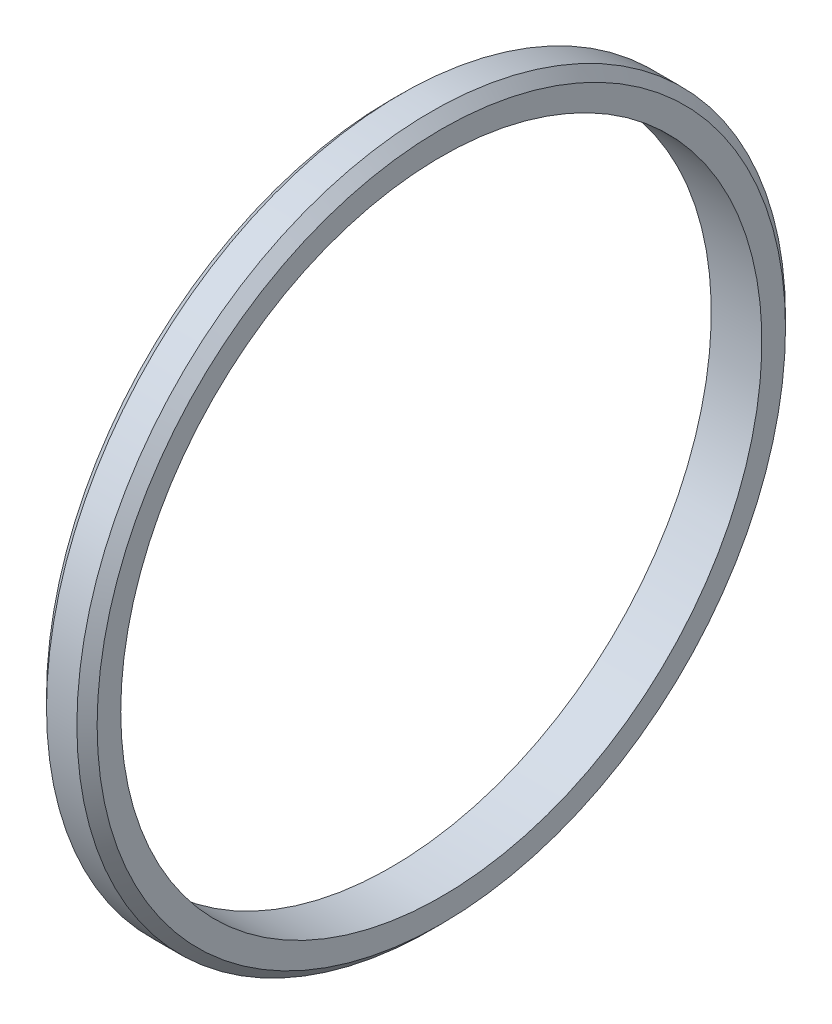
SolidWorks part; units mm, degrees
material "1060 Сплав"
ref_plane "Спереди" through (0, 0, 0) normal (0, 0, 1) x (1, 0, 0)
ref_plane "Сверху" through (0, 0, 0) normal (0, 1, 0) x (1, 0, 0)
ref_plane "Справа" through (0, 0, 0) normal (1, 0, 0) x (0, 0, -1)
sketch "Эскиз1" plane through (0, 0, 0) normal (0, 0, 1) x (1, 0, 0)
  line L0 (0, 0) -> (19729.2618, 0) construction
  line L1 (0, 19) -> (3, 19)
  line L2 (3, 19) -> (3, 21)
  line L3 (3, 21) -> (0, 21)
  line L4 (0, 21) -> (0, 19)
  line L5 (0, 19) -> (0, 0) construction
  dimension "D1" = 42
  dimension "D2" = 3
  dimension "D3" = 2
revolve "Повернуть1" add sketch "Эскиз1" angle 360 about L0
chamfer "Фаска1" distance 0.6 angle 45 2 edges at (0, 0, 21) (3, 0, 21)
